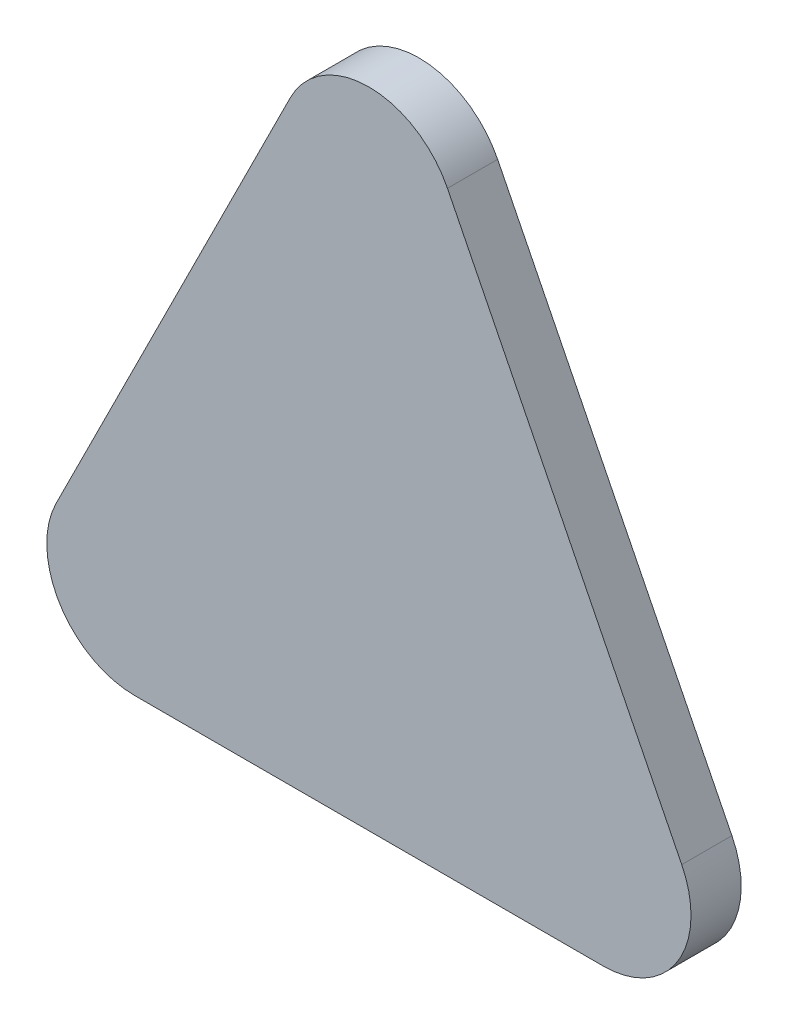
SolidWorks part; units mm, degrees
ref_plane "Front Plane" through (0, 0, 0) normal (0, 0, 1) x (1, 0, 0)
ref_plane "Top Plane" through (0, 0, 0) normal (0, 1, 0) x (1, 0, 0)
ref_plane "Right Plane" through (0, 0, 0) normal (1, 0, 0) x (0, 0, -1)
sketch "Sketch1" plane through (0, 0, 0) normal (0, 0, 1) x (1, 0, 0)
  line L0 (7.9515, 60.2971) -> (31.6671, 12.8657)
  line L1 (23.7157, 0) -> (-23.7157, 0)
  line L2 (-31.6671, 12.8657) -> (-7.9515, 60.2971)
  arc A1 (-23.7157, 0) -> (-31.6671, 12.8657) centre (-23.7157, 8.89) cw
  arc A2 (31.6671, 12.8657) -> (23.7157, 0) centre (23.7157, 8.89) cw
  arc A3 (7.9515, 60.2971) -> (-7.9515, 60.2971) centre (0, 56.3214) ccw
  circle A4 centre (0, 56.3214) radius 6.35
  circle A5 centre (-23.7157, 8.89) radius 6.35
  circle A6 centre (23.7157, 8.89) radius 6.35
  point P6 (-38.1, 0)
  point P9 (38.1, 0)
  point P14 (0, 76.2)
  dimension "D1" = 76.2
  dimension "D2" = 76.2
  dimension "D3" = 8.89
  dimension "D4" = 2.54
extrude "Boss-Extrude1" add sketch "Sketch1" along normal blind 5.08 contours L2 A3 L0 A2 L1 A1
